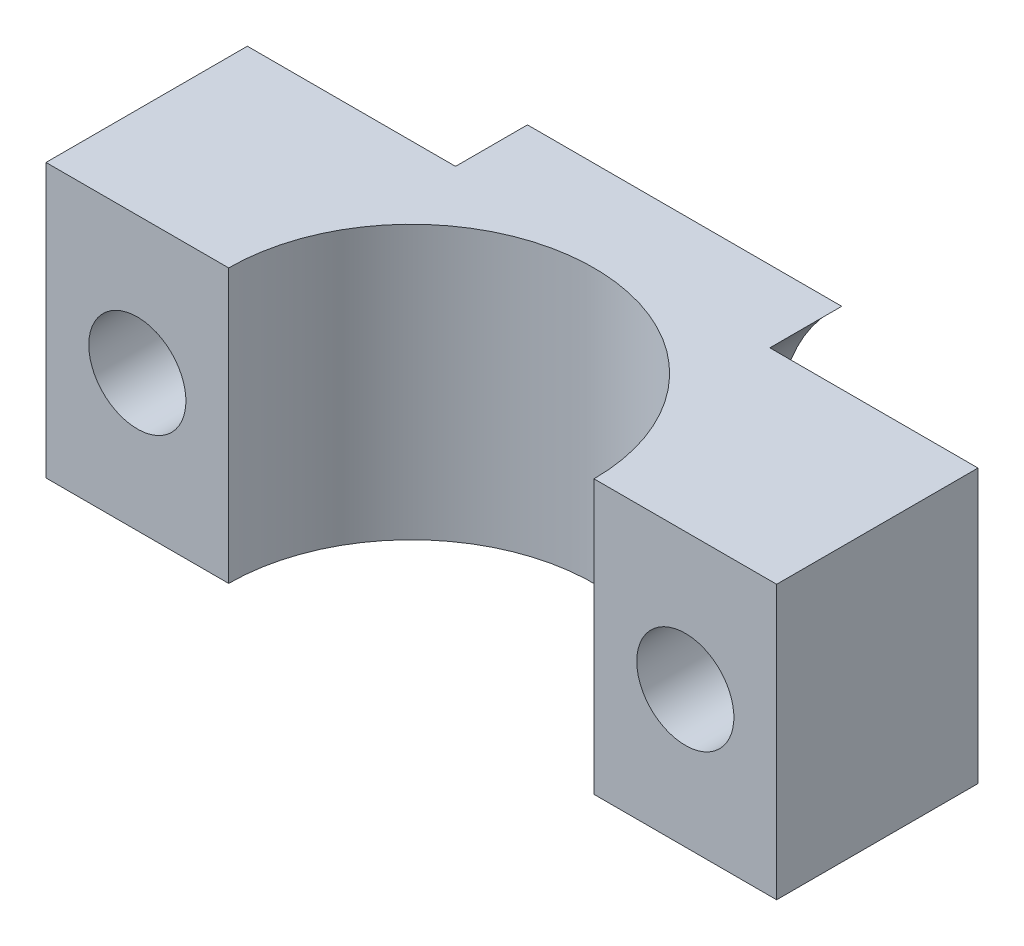
SolidWorks part; units mm, degrees
ref_plane "Front Plane" through (0, 0, 0) normal (0, 0, 1) x (1, 0, 0)
ref_plane "Top Plane" through (0, 0, 0) normal (0, 1, 0) x (1, 0, 0)
ref_plane "Right Plane" through (0, 0, 0) normal (1, 0, 0) x (0, 0, -1)
sketch "Sketch1" plane through (0, 0, 0) normal (0, 1, 0) x (1, 0, 0)
  line L1 (25.4, 0) -> (-25.4, 0)
  line L2 (25.4, 0) -> (25.4, 19)
  line L3 (25.4, 19) -> (-25.4, 19)
  line L4 (-25.4, 0) -> (-25.4, 19)
  circle A0 centre (0, 0) radius 12.7
  dimension "D3" = 25.4
  dimension "D1" = 50.8
  dimension "D2" = 19
extrude "Boss-Extrude1" add sketch "Sketch1" along normal blind 19 contours A0 L1 L2 L3 L4
sketch "Sketch5" plane through (0, 0, -19) normal (0, 0, -1) x (-1, 0, 0)
  line L0 (-25.4, 9.5) -> (-12.7, 9.5) construction
  line L1 (-25.4, 19) -> (-25.4, 0) construction
  line L2 (25.4, 19) -> (25.4, 0) construction
  line L7 (12.7, 9.5) -> (25.4, 9.5) construction
  point P6 (-19.05, 9.5)
  point P7 (19.05, 9.5)
hole_wizard "CBORE for M12 Hex Head Cap Screw2" positions "3DSketch3" profile "Sketch6" counterbore size "M12" standard "ISO" end condition through all
sketch3d "3DSketch3"
  point P0 (19.05, 9.5, -19)
  point P3 (-19.05, 9.5, -19)
sketch "Sketch6" plane through (19.05, 9.5, -19) normal (1, 0, 0) x (0, 1, 0)
  line L0 (0, 0) -> (0, 19)
  line L1 (0, 19) -> (3.375, 19)
  line L3 (3.375, 19) -> (3.375, 5)
  line L4 (3.375, 5) -> (12.5, 5)
  line L5 (12.5, 5) -> (12.5, 0)
  line L7 (12.5, 0) -> (0, 0)
  line L11 (0, -6.35) -> (0, 107.95) construction
  dimension "Thru Hole Dia." = 6.75
  dimension "Thru Hole Depth" = 19
  dimension "C'Bore Dia." = 25
  dimension "C'Bore Depth" = 5
